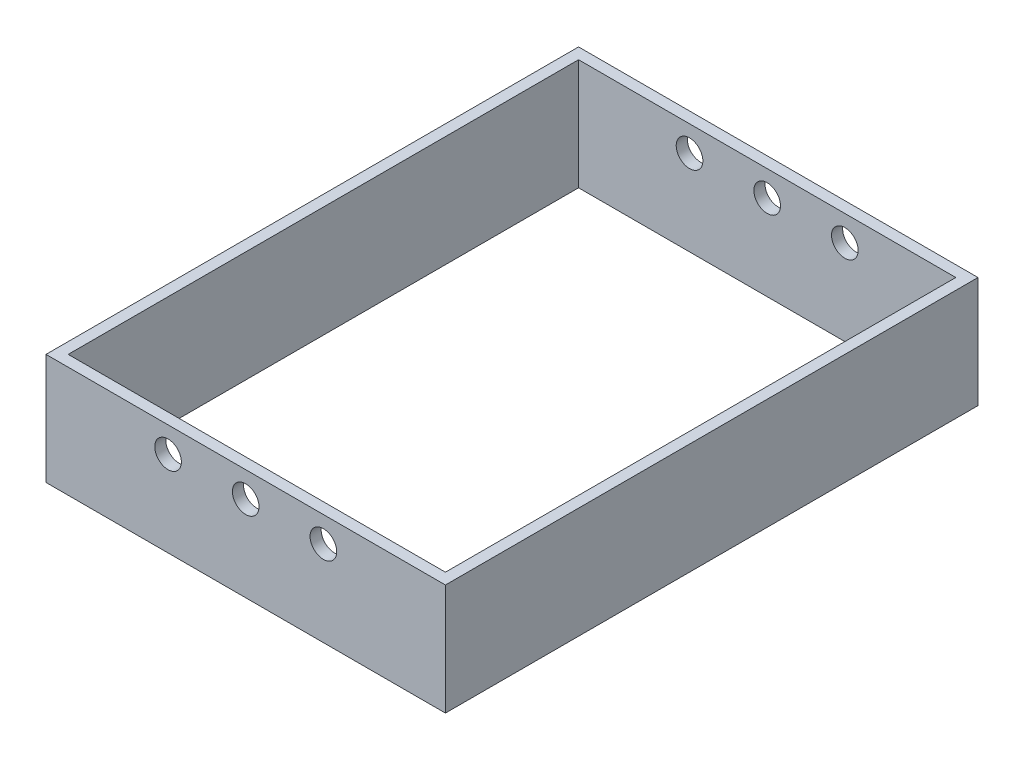
SolidWorks part; units mm, degrees
ref_plane "Alzado" through (0, 0, 0) normal (0, 0, 1) x (1, 0, 0)
ref_plane "Planta" through (0, 0, 0) normal (0, 1, 0) x (1, 0, 0)
ref_plane "Vista lateral" through (0, 0, 0) normal (1, 0, 0) x (0, 0, -1)
sketch "Croquis1" plane through (0, 0, 0) normal (0, 1, 0) x (1, 0, 0)
  line L1 (-90, -120) -> (90, -120)
  line L2 (-90, -120) -> (-90, 120)
  line L3 (-90, 120) -> (90, 120)
  line L4 (90, -120) -> (90, 120)
  line L5 (-90, -120) -> (90, 120) construction
  line L6 (-90, 120) -> (90, -120) construction
  line L11 (-85, 115) -> (85, 115)
  line L12 (-85, 115) -> (-85, -115)
  line L13 (-85, -115) -> (85, -115)
  line L14 (85, 115) -> (85, -115)
  line L15 (-85, 115) -> (85, -115) construction
  line L16 (-85, -115) -> (85, 115) construction
  point P0 (0, 0)
  point P6 (0, 0)
  point P7 (0, 0)
  dimension "D1" = 240
  dimension "D2" = 180
  dimension "D3" = 170
  dimension "D4" = 230
extrude "Saliente-Extruir1" add sketch "Croquis1" along normal blind 50
sketch "Croquis2" plane through (0, 0, 120) normal (0, 0, 1) x (1, 0, 0)
  line L0 (-41, 38.5) -> (41, 38.5) construction
  line L3 (0, 50) -> (0, 0) construction
  line L4 (-90, 50) -> (90, 50) construction
  line L5 (-35, 50) -> (-35, 0) construction
  line L6 (35, 50) -> (35, 0) construction
  circle A0 centre (-35, 38.5) radius 6
  circle A1 centre (0, 38.5) radius 6
  circle A2 centre (35, 38.5) radius 6
  dimension "D3" = 12
  dimension "D4" = 12
  dimension "D5" = 12
  dimension "D6" = 11.5
  dimension "D1" = 35
  dimension "D2" = 35
extrude "Cortar-Extruir1" cut sketch "Croquis2" against normal through all
sketch "Croquis3" plane through (0, 50, 0) normal (0, 1, 0) x (1, 0, 0)
  line L4 (90, -120) -> (90, 120)
  line L5 (90, 120) -> (-90, 120)
  line L6 (-90, 120) -> (-90, -120)
  line L7 (-90, -120) -> (90, -120)
  line L8 (90, -120) -> (90, 120)
  line L9 (90, 120) -> (-90, 120)
  line L10 (-90, 120) -> (-90, -120)
  line L11 (-90, -120) -> (90, -120)
  dimension "D1" = 0
extrude "Cortar-Extruir2" [suppressed] cut sketch "Croquis3" against normal blind 15
